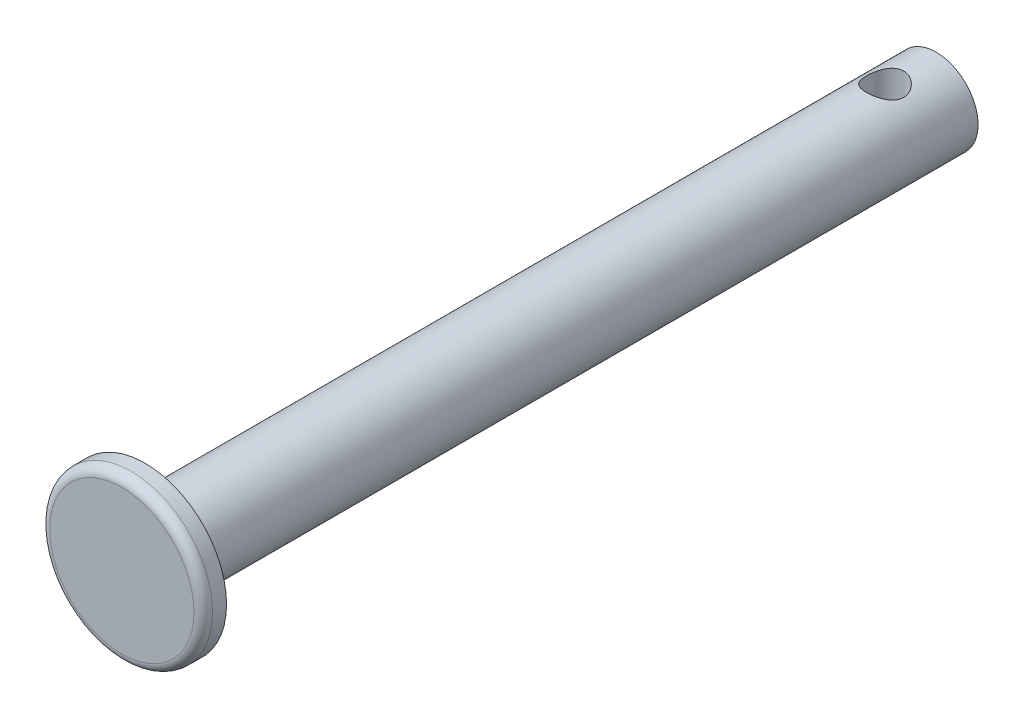
SolidWorks part; units mm, degrees
material "1.0558 (G300)"
ref_plane "Ön Düzlem" through (0, 0, 0) normal (0, 0, 1) x (1, 0, 0)
ref_plane "Üst Düzlem" through (0, 0, 0) normal (0, 1, 0) x (1, 0, 0)
ref_plane "Sağ Düzlem" through (0, 0, 0) normal (1, 0, 0) x (0, 0, -1)
sketch "Çizim1" plane through (0, 0, 0) normal (0, 0, 1) x (1, 0, 0)
  circle A0 centre (0, 0) radius 17.5
  dimension "D1" = 35
extrude "Yükseklik-Ekstrüzyon1" add sketch "Çizim1" along normal blind 5
fillet "Radyus1" radius 2 1 edges at (17.5, 0, 5)
sketch "Çizim2" plane through (0, 0, 0) normal (0, 0, -1) x (-1, 0, 0)
  circle A0 centre (0, 0) radius 9
  dimension "D1" = 18
extrude "Yükseklik-Ekstrüzyon2" add sketch "Çizim2" along normal blind 170
sketch "Çizim3" plane through (0, 0, 0) normal (0, 1, 0) x (1, 0, 0)
  line L0 (0, 159) -> (0, 163) construction
  line L1 (9, 170) -> (-9, 170) construction
  circle A0 centre (0, 159) radius 4
  dimension "D2" = 8
  dimension "D1" = 7
extrude "Kes-Ekstrüzyon1" cut sketch "Çizim3" against normal mid plane 170 contours A0
